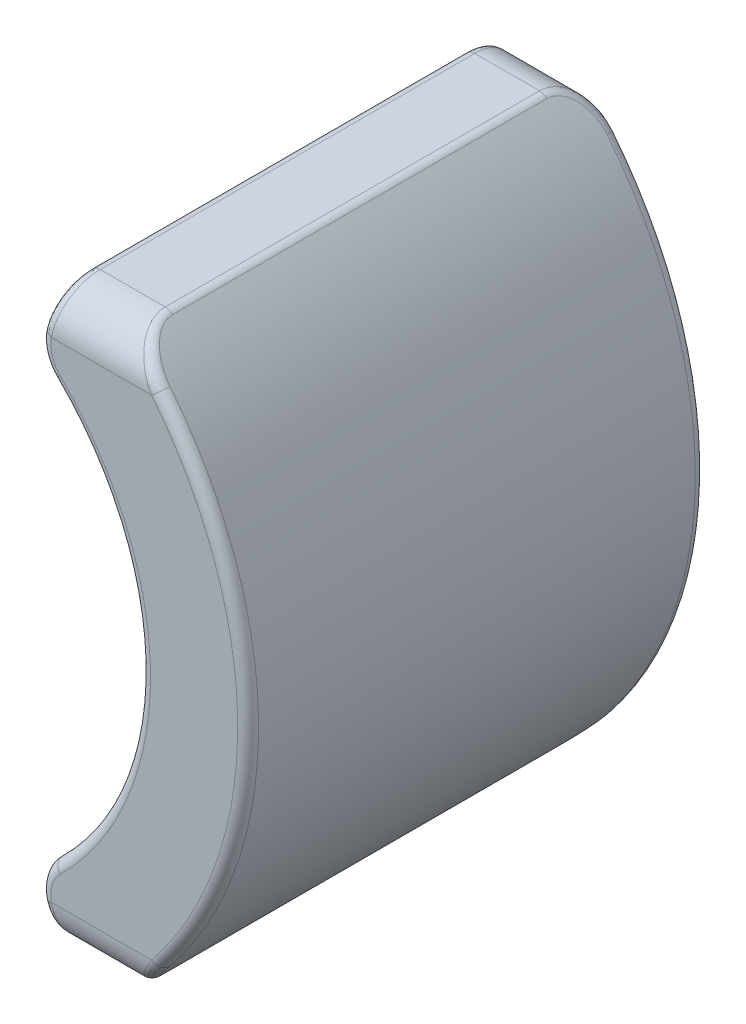
SolidWorks part; units mm, degrees
ref_plane "Ön Düzlem" through (0, 0, 0) normal (0, 0, 1) x (1, 0, 0)
ref_plane "Üst Düzlem" through (0, 0, 0) normal (0, 1, 0) x (1, 0, 0)
ref_plane "Sağ Düzlem" through (0, 0, 0) normal (1, 0, 0) x (0, 0, -1)
sketch "Sketch1" plane through (0, 0, 0) normal (0, 0, 1) x (1, 0, 0)
  line L0 (0, 0) -> (9.63, 0) construction
  line L1 (6.7381, -6.88) -> (4.8781, -6.88)
  line L2 (4.8781, -6.88) -> (4.5318, -5.38)
  line L3 (4.8781, 6.88) -> (4.5318, 5.38)
  line L4 (6.7381, 6.88) -> (4.8781, 6.88)
  arc A0 (6.7381, 6.88) -> (6.7381, -6.88) centre (0, 0) cw
  arc A1 (4.5318, 5.38) -> (4.5318, -5.38) centre (0, 0) cw
  point P6 (9.63, 0)
  dimension "D1" = 9.63
  dimension "D2" = 1.86
  dimension "D3" = 103
  dimension "D4" = 1.5
  dimension "D5" = 6.88
extrude "Boss-Extrude1" add sketch "Sketch1" along normal blind 11
fillet "Fillet1" radius 1 2 edges at (4.5318, -5.38, 5.5) (4.5318, 5.38, 5.5)
fillet "Fillet2" radius 1 4 edges at (5.8081, -6.88, 0) (5.8081, -6.88, 11) (5.8081, 6.88, 11) (5.8081, 6.88, 0)
fillet "Fillet3" radius 0.25 24 edges at (4.8161, -6.6112, 0.3178) (4.8781, -6.88, 5.5) (4.8161, -6.6112, 10.6822) (4.6879, -5.4113, 11) (7.0343, 0, 11) (4.6879, 5.4113, 11) (4.8161, 6.6112, 10.6822) (4.8781, 6.88, 5.5) (4.8161, 6.6112, 0.3178) (6.8685, -6.7498, 0.5066) (6.7381, -6.88, 5.5) (6.9882, -6.6258, 10.6661) (9.63, 0, 11) (6.8685, 6.7498, 10.4934) (6.7381, 6.88, 5.5) (6.9882, 6.6258, 0.3339) (4.6879, 5.4113, 0) (7.0343, 0, 0) (4.6879, -5.4113, 0) (9.63, 0, 0)
